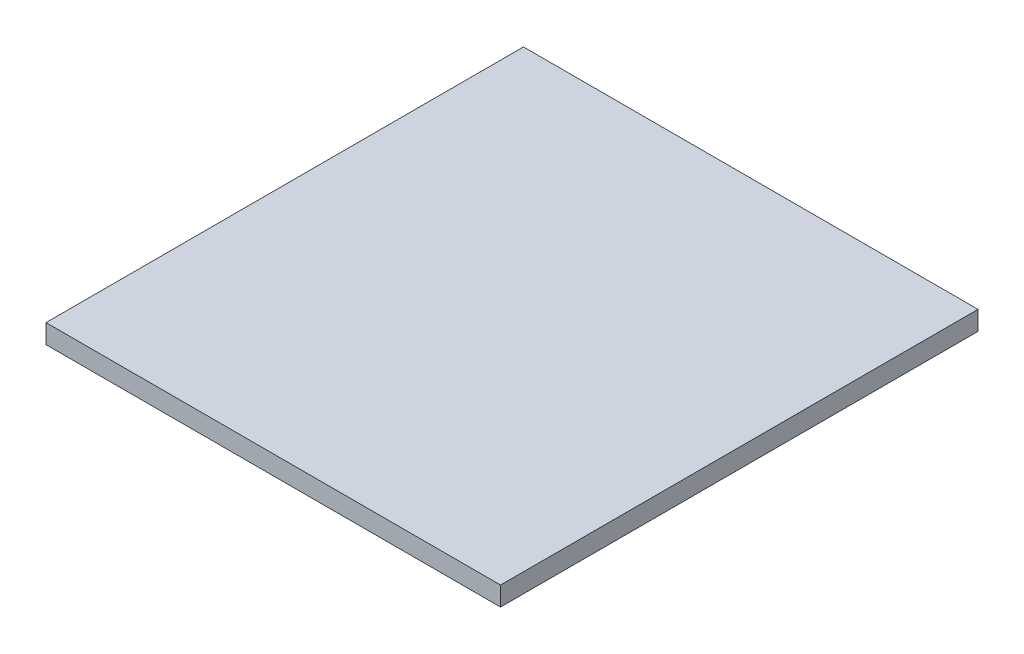
SolidWorks part; units mm, degrees
ref_plane "Спереди" through (0, 0, 0) normal (0, 0, 1) x (1, 0, 0)
ref_plane "Сверху" through (0, 0, 0) normal (0, 1, 0) x (1, 0, 0)
ref_plane "Справа" through (0, 0, 0) normal (1, 0, 0) x (0, 0, -1)
sketch "Эскиз2" plane through (0, 0, 0) normal (0, 1, 0) x (1, 0, 0)
  line L1 (0, 0) -> (238, 0)
  line L2 (0, 0) -> (0, 250)
  line L3 (0, 250) -> (238, 250)
  line L4 (238, 0) -> (238, 250)
extrude "Бобышка-Вытянуть1" add sketch "Эскиз2" along normal blind 10
